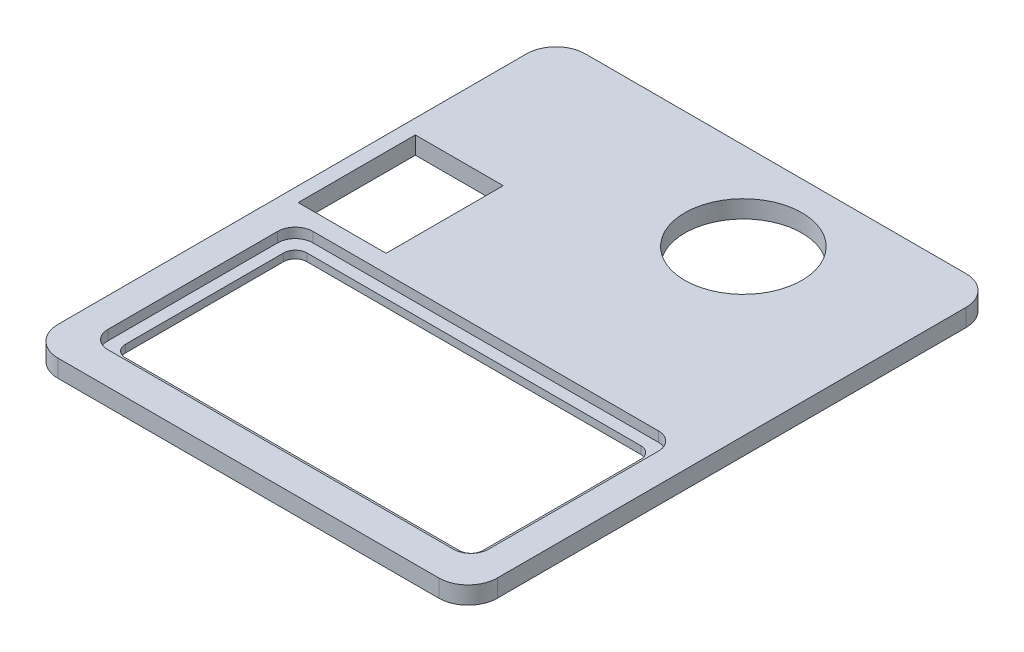
SolidWorks part; units mm, degrees
ref_plane "Front Plane" through (0, 0, 0) normal (0, 0, 1) x (1, 0, 0)
ref_plane "Top Plane" through (0, 0, 0) normal (0, 1, 0) x (1, 0, 0)
ref_plane "Right Plane" through (0, 0, 0) normal (1, 0, 0) x (0, 0, -1)
sketch "Sketch1" plane through (0, 0, 0) normal (0, 1, 0) x (1, 0, 0)
  line L1 (5, 0) -> (70, 0)
  line L2 (0, 5) -> (0, 85)
  line L3 (5, 90) -> (70, 90)
  line L4 (75, 5) -> (75, 85)
  arc A0 (70, 0) -> (75, 5) centre (70, 5) ccw
  arc A1 (5, 0) -> (0, 5) centre (5, 5) cw
  arc A2 (70, 90) -> (75, 85) centre (70, 85) cw
  arc A3 (0, 85) -> (5, 90) centre (5, 85) cw
  point P9 (0, 0)
  point P12 (75, 90)
  point P15 (0, 90)
  dimension "D3" = 5
  dimension "D1" = 90
  dimension "D2" = 75
extrude "Boss-Extrude1" add sketch "Sketch1" along normal blind 3
sketch "Sketch2" plane through (0, 0, 0) normal (0, 1, 0) x (1, 0, 0)
  line L0 (37.5, 0) -> (37.5, 90) construction
  line L1 (5, 0) -> (70, 0) construction
  line L2 (70, 90) -> (5, 90) construction
  line L3 (0, 23) -> (75, 23) construction
  line L4 (0, 85) -> (0, 5) construction
  line L5 (75, 5) -> (75, 85) construction
  line L6 (19, 75) -> (75, 75) construction
  line L7 (8, 5.5) -> (67, 5.5)
  line L8 (5, 8.5) -> (5, 37.5)
  line L9 (8, 40.5) -> (67, 40.5)
  line L10 (70, 8.5) -> (70, 37.5)
  line L11 (5, 5.5) -> (70, 40.5) construction
  line L12 (5, 40.5) -> (70, 5.5) construction
  line L14 (2.5, 43.5) -> (17.5, 43.5)
  line L15 (2.5, 43.5) -> (2.5, 63.5)
  line L16 (2.5, 63.5) -> (17.5, 63.5)
  line L17 (17.5, 43.5) -> (17.5, 63.5)
  arc A0 (67, 5.5) -> (70, 8.5) centre (67, 8.5) ccw
  arc A1 (67, 40.5) -> (70, 37.5) centre (67, 37.5) cw
  arc A2 (5, 37.5) -> (8, 40.5) centre (8, 37.5) cw
  arc A3 (8, 5.5) -> (5, 8.5) centre (8, 8.5) cw
  circle A4 centre (47, 75) radius 10
  point P12 (37.5, 23)
  dimension "D3" = 3
  dimension "D6" = 20
  dimension "D7" = 28
  dimension "D1" = 23
  dimension "D2" = 35
  dimension "D4" = 5
  dimension "D5" = 75
  dimension "D8" = 20
  dimension "D9" = 15
  dimension "D10" = 2.5
  dimension "D11" = 3
extrude "Cut-Extrude4" cut sketch "Sketch2" against normal blind 3 and the other way blind 7 contours L8 A2 L9 A1 L10 A0 L7 A3 | A4 | L15 L14 L17 L16
sketch "Sketch6" plane through (0, 0, 0) normal (0, 1, 0) x (1, 0, 0)
  line L16 (67, 5.5) -> (8, 5.5) construction
  line L17 (5, 40.5) -> (70, 40.5)
  line L18 (5, 40.5) -> (5, 5.5)
  line L19 (5, 5.5) -> (70, 5.5)
  line L20 (70, 40.5) -> (70, 5.5)
  line L21 (9, 38.5) -> (66, 38.5)
  line L22 (7, 36.5) -> (7, 9.5)
  line L23 (9, 7.5) -> (66, 7.5)
  line L24 (68, 36.5) -> (68, 9.5)
  line L25 (67, 40.5) -> (8, 40.5) construction
  line L26 (5, 37.5) -> (5, 8.5) construction
  arc A0 (7, 9.5) -> (9, 7.5) centre (9, 9.5) ccw
  arc A1 (66, 7.5) -> (68, 9.5) centre (66, 9.5) ccw
  arc A2 (66, 38.5) -> (68, 36.5) centre (66, 36.5) cw
  arc A3 (9, 38.5) -> (7, 36.5) centre (9, 36.5) ccw
  point P23 (67, 8.5)
  point P28 (8, 37.5)
  dimension "D5" = 2
  dimension "D1" = 3
  dimension "D2" = 0
  dimension "D3" = 0
  dimension "D4" = 0
  dimension "D6" = 2
  dimension "D7" = 2
  dimension "D8" = 2
  dimension "D9" = 2
extrude "Boss-Extrude5" add sketch "Sketch6" along normal blind 1.3
